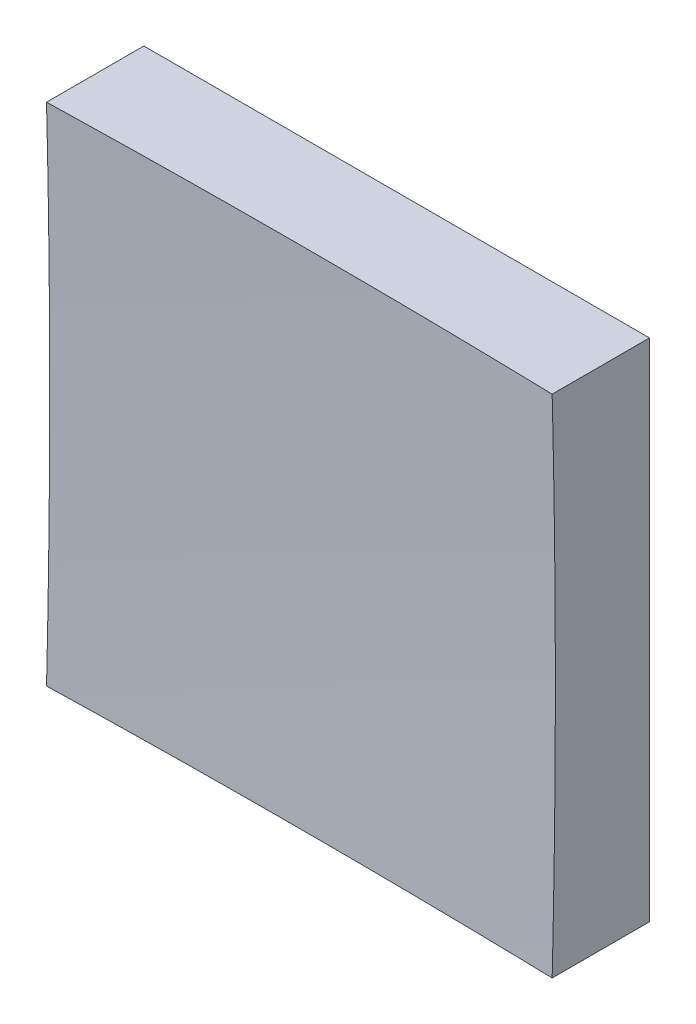
SolidWorks part; units mm, degrees
ref_plane "前视基准面" through (0, 0, 0) normal (0, 0, 1) x (1, 0, 0)
ref_plane "上视基准面" through (0, 0, 0) normal (0, 1, 0) x (1, 0, 0)
ref_plane "右视基准面" through (0, 0, 0) normal (1, 0, 0) x (0, 0, -1)
sketch "草图1" plane through (0, 0, 0) normal (0, 0, 1) x (1, 0, 0)
  line L1 (-25, 25) -> (25, 25)
  line L2 (-25, 25) -> (-25, -25)
  line L3 (-25, -25) -> (25, -25)
  line L4 (25, 25) -> (25, -25)
  line L5 (-25, 25) -> (25, -25) construction
  line L6 (-25, -25) -> (25, 25) construction
  point P0 (0, 0)
  dimension "D1" = 50
  dimension "D2" = 50
extrude "凸台-拉伸1" add sketch "草图1" along normal blind 50 contours L2 L3 L4 L1
sketch "草图2" plane through (0, 0, 0) normal (0, 1, 0) x (1, 0, 0)
  line L0 (-7.4603, -9) -> (7.3192, -9) construction
  line L1 (0, 0) -> (0, -12.1749) construction
  line L2 (974.8455, -786.1181) -> (0, -786.1181)
  line L3 (0, -786.1181) -> (0, -9)
  arc A1 (974.8455, -786.1181) -> (0, -9) centre (0, -1009) ccw
  dimension "D2" = 2000
  dimension "D1" = 9
revolve "切除-旋转2" cut sketch "草图2" angle 360 about L3
